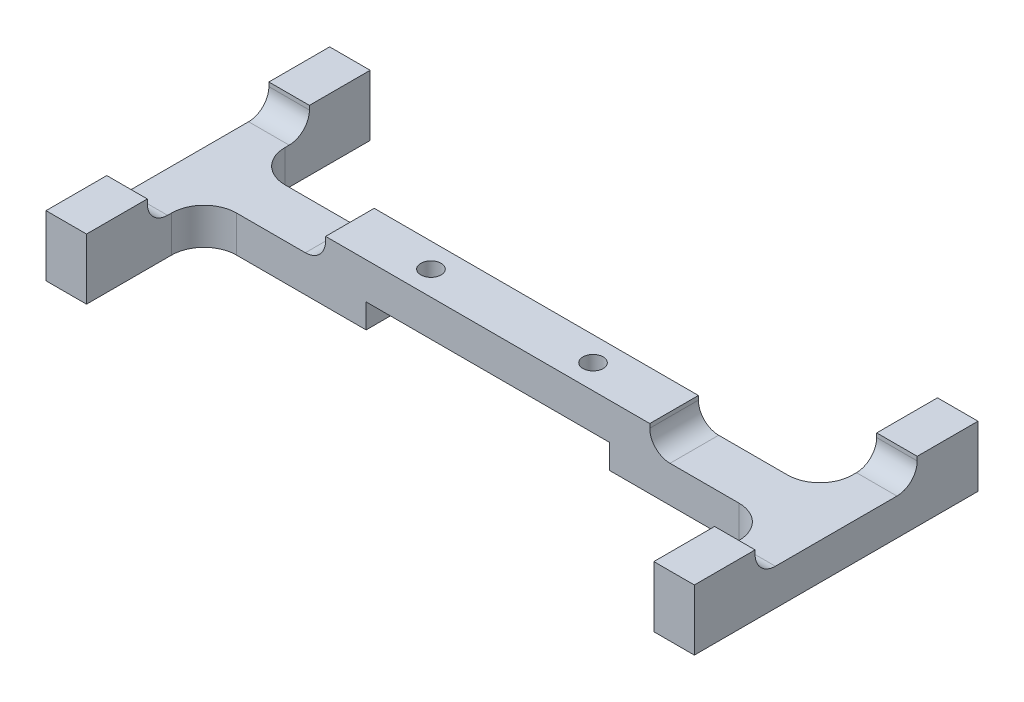
SolidWorks part; units mm, degrees
ref_plane "Front Plane" through (0, 0, 0) normal (0, 0, 1) x (1, 0, 0)
ref_plane "Top Plane" through (0, 0, 0) normal (0, 1, 0) x (1, 0, 0)
ref_plane "Right Plane" through (0, 0, 0) normal (1, 0, 0) x (0, 0, -1)
sketch "Sketch1" plane through (0, 0, 0) normal (0, 1, 0) x (1, 0, 0)
  line L1 (-50.8, -22.225) -> (50.8, -22.225)
  line L2 (-50.8, -22.225) -> (-50.8, 22.225)
  line L3 (-50.8, 22.225) -> (50.8, 22.225)
  line L4 (50.8, -22.225) -> (50.8, 22.225)
  line L5 (-50.8, -22.225) -> (50.8, 22.225) construction
  line L6 (-50.8, 22.225) -> (50.8, -22.225) construction
  point P0 (0, 0)
  dimension "D1" = 101.6
  dimension "D2" = 44.45
extrude "Boss-Extrude1" add sketch "Sketch1" along normal blind 9.525
sketch "Sketch2" plane through (0, 9.525, 0) normal (0, 1, 0) x (1, 0, 0)
  line L0 (-50.8, -22.225) -> (50.8, -22.225) construction
  line L1 (-44.45, -22.225) -> (44.45, -22.225)
  line L2 (-44.45, -22.225) -> (-44.45, -3.81)
  line L3 (-44.45, -3.81) -> (44.45, -3.81)
  line L4 (44.45, -22.225) -> (44.45, -3.81)
  line L5 (-50.8, 22.225) -> (-50.8, -22.225) construction
  line L6 (50.8, -22.225) -> (50.8, 22.225) construction
  dimension "D1" = 6.35
  dimension "D2" = 6.35
  dimension "D3" = 3.81
extrude "Cut-Extrude1" cut sketch "Sketch2" against normal through all
mirror "Mirror1" about plane through (0, 0, 0) normal (0, 0, 1) of "Cut-Extrude1"
fillet "Fillet1" radius 5.08 4 edges at (44.45, 4.7625, -3.81) (44.45, 4.7625, 3.81) (-44.45, 4.7625, 3.81) (-44.45, 4.7625, -3.81)
sketch "Sketch3" plane through (0, 9.525, 0) normal (0, 1, 0) x (1, 0, 0)
  line L0 (-50.8, 22.225) -> (-50.8, -22.225) construction
  line L1 (-50.8, 12.7) -> (-25.4, 12.7)
  line L2 (-50.8, 12.7) -> (-50.8, -12.7)
  line L3 (-50.8, -12.7) -> (-25.4, -12.7)
  line L4 (-25.4, 12.7) -> (-25.4, -12.7)
  dimension "D1" = 12.7
  dimension "D2" = 12.7
  dimension "D3" = 25.4
extrude "Cut-Extrude2" cut sketch "Sketch3" against normal blind 3.81
mirror "Mirror2" about plane through (0, 0, 0) normal (1, 0, 0) of "Cut-Extrude2"
fillet "Fillet2" radius 3.175 6 edges at (-25.4, 5.715, 0) (25.4, 5.715, 0) (47.625, 5.715, 12.7) (47.625, 5.715, -12.7) (-47.625, 5.715, 12.7) (-47.625, 5.715, -12.7)
sketch "Sketch4" plane through (0, 0, 0) normal (0, -1, 0) x (1, 0, 0)
  circle A0 centre (-12.7, 0) radius 1.5875
  dimension "D1" = 3.175
  dimension "D2" = 12.7
extrude "Cut-Extrude3" cut sketch "Sketch4" against normal through all
sketch "Sketch5" plane through (0, 0, 0) normal (0, -1, 0) x (1, 0, 0)
  line L0 (39.37, 3.81) -> (-39.37, 3.81) construction
  line L1 (-19.05, 3.81) -> (19.05, 3.81)
  line L2 (-19.05, 3.81) -> (-19.05, -3.81)
  line L3 (-19.05, -3.81) -> (19.05, -3.81)
  line L4 (19.05, 3.81) -> (19.05, -3.81)
  line L5 (39.37, -3.81) -> (-39.37, -3.81) construction
  dimension "D1" = 19.05
  dimension "D2" = 19.05
extrude "Cut-Extrude4" cut sketch "Sketch5" against normal blind 3.81
mirror "Mirror3" about plane through (0, 0, 0) normal (1, 0, 0) of "Cut-Extrude3"
